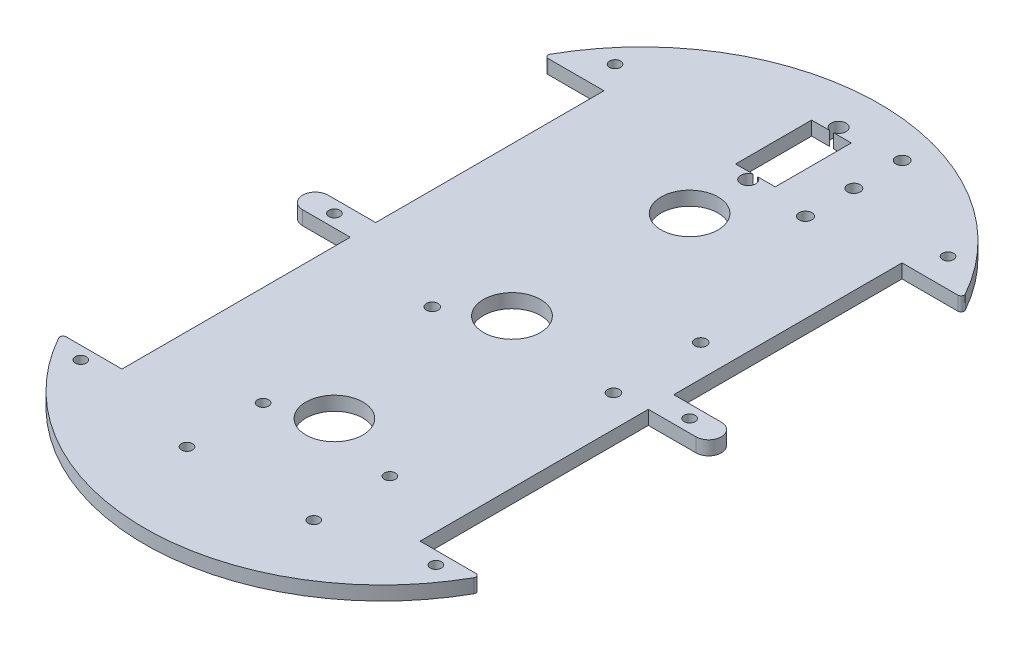
SolidWorks part; units mm, degrees
material "ABS PC"
ref_plane "Front Plane" through (0, 0, 0) normal (0, 0, 1) x (1, 0, 0)
ref_plane "Top Plane" through (0, 0, 0) normal (0, 1, 0) x (1, 0, 0)
ref_plane "Right Plane" through (0, 0, 0) normal (1, 0, 0) x (0, 0, -1)
sketch "Sketch2" plane through (0, 0, 0) normal (0, 1, 0) x (1, 0, 0)
  line L1 (-66, 116) -> (66, 116)
  line L2 (-66, 116) -> (-66, -116)
  line L3 (-66, -116) -> (66, -116)
  line L4 (66, 116) -> (66, -116)
  point P4 (66, 0)
  point P6 (0, 116)
  dimension "D1" = 132
  dimension "D2" = 232
extrude "Plate Size" add sketch "Sketch2" along normal blind 4.4
sketch "Sketch4" plane through (0, 0, 0) normal (0, 1, 0) x (1, 0, 0)
  line L0 (-66, 116) -> (-66, -116) construction
  line L1 (66, 116) -> (66, -116) construction
  line L2 (0, -40.9051) -> (0, 40.9051) construction
  line L4 (-64.6, 76) -> (-47, 76)
  line L6 (-62, 4) -> (-47, 4)
  line L7 (-47, 76) -> (-47, 4)
  line L8 (-47, -4) -> (-47, 4) construction
  line L9 (64.6, 76) -> (47, 76)
  line L11 (62, 4) -> (47, 4)
  line L12 (47, 76) -> (47, 4)
  line L13 (64.6, -76) -> (47, -76)
  line L15 (62, -4) -> (47, -4)
  line L16 (47, -76) -> (47, -4)
  line L17 (-47, -76) -> (-64.6, -76)
  line L18 (-47, -76) -> (-47, -4)
  line L19 (-47, -4) -> (-62, -4)
  line L21 (47, -4) -> (47, 4) construction
  line L23 (-47, 40) -> (47, 40) construction
  line L24 (0, -2.475) -> (0, 2.475) construction
  arc A0 (65.473, 77.4878) -> (-65.473, 77.4878) centre (0, 40.9051) ccw
  arc A1 (-65.473, -77.4878) -> (65.473, -77.4878) centre (0, -40.9051) ccw
  arc A2 (-62, 4) -> (-62, -4) centre (-62, 0) ccw
  arc A3 (62, -4) -> (62, 4) centre (62, 0) ccw
  arc A4 (-64.6, -76) -> (-65.473, -77.4878) centre (-64.6, -77) ccw
  arc A5 (65.473, -77.4878) -> (64.6, -76) centre (64.6, -77) ccw
  arc A6 (64.6, 76) -> (65.473, 77.4878) centre (64.6, 77) ccw
  arc A7 (-65.473, 77.4878) -> (-64.6, 76) centre (-64.6, 77) ccw
  point P2 (0, 0)
  point P33 (-47, 0)
  point P39 (0, 40)
  dimension "D1" = 150
  dimension "D2" = 231.8102
  dimension "D6" = 2
  dimension "D3" = 72
  dimension "D4" = 8
  dimension "D5" = 94
extrude "Outer Profile" cut sketch "Sketch4" along normal through all flip side to cut
hole_wizard "M3 Clearance Hole1" positions "Sketch5" profile "Sketch6" hole size "M3" standard "ANSI Metric" end condition through all
sketch "Sketch5" plane through (0, 0, 0) normal (0, 1, 0) x (1, 0, 0)
  line L1 (-56, -80) -> (56, -80) construction
  line L5 (0, -2.42) -> (0, 2.42) construction
  line L7 (-2.42, 0) -> (2.42, 0) construction
  line L8 (-52.5, 85) -> (52.5, 85) construction
  line L10 (56, 0) -> (-56, 0) construction
  circle A0 centre (-56, -80) radius 1.75 construction
  point P0 (-56, -80)
  point P159 (56, -80)
  point P161 (0, -80)
  point P171 (-52.5, 85)
  point P177 (52.5, 85)
  point P179 (0, 85)
  point P184 (-56, 0)
  point P186 (56, 0)
  point P192 (0, 0)
  dimension "D1" = 80
  dimension "D3" = 3.5
  dimension "D2" = 56
  dimension "D4" = 52.5
  dimension "D5" = 85
sketch "Sketch6" plane through (-56, 0, 80) normal (1, 0, 0) x (0, 0, -1)
  line L0 (0, 0) -> (0, 4.4)
  line L1 (0, 4.4) -> (1.75, 4.4)
  line L2 (1.75, 4.4) -> (1.75, 0)
  line L5 (1.75, 0) -> (0, 0)
  line L11 (0, -6.35) -> (0, 107.95) construction
  dimension "Thru Hole Dia." = 3.5
  dimension "Thru Hole Depth" = 4.4
hole_wizard "Ø18.0 (18) Diameter Hole4" positions "Sketch9" profile "Sketch10" hole size "Ø18.0" standard "ANSI Metric" end condition through all
sketch "Sketch9" plane through (0, 0, 0) normal (0, 1, 0) x (1, 0, 0)
  line L0 (0, -2.42) -> (0, 2.42) construction
  line L1 (0, -56) -> (0, 56) construction
  line L3 (-2.42, 0) -> (2.42, 0) construction
  point P0 (0, 56)
  point P2 (0, -56)
  point P10 (0, 0)
  dimension "D1" = 56
sketch "Sketch10" plane through (0, 0, -56) normal (1, 0, 0) x (0, 0, -1)
  line L0 (0, 0) -> (0, 4.4)
  line L1 (0, 4.4) -> (9, 4.4)
  line L2 (9, 4.4) -> (9, 0)
  line L5 (9, 0) -> (0, 0)
  line L11 (0, -6.35) -> (0, 107.95) construction
  dimension "Thru Hole Dia." = 18
  dimension "Thru Hole Depth" = 4.4
hole_wizard "M3 Clearance Hole2" positions "Sketch11" profile "Sketch12" hole size "M3" standard "ANSI Metric" end condition through all
sketch "Sketch11" plane through (0, 0, 0) normal (0, 1, 0) x (1, 0, 0)
  line L1 (24.5, -87) -> (-15.5, -87) construction
  line L2 (24.5, -87) -> (24.5, -63) construction
  line L3 (24.5, -63) -> (-15.5, -63) construction
  line L4 (-15.5, -87) -> (-15.5, -63) construction
  line L5 (0, -2.42) -> (0, 2.42) construction
  line L7 (-2.42, 0) -> (2.42, 0) construction
  circle A0 centre (24.5, -87) radius 2 construction
  circle A1 centre (-15.5, -63) radius 2 construction
  point P0 (24.5, -87)
  point P2 (-15.5, -63)
  point P110 (-15.5, -87)
  point P113 (24.5, -63)
  dimension "D1" = 4
  dimension "D3" = 87
  dimension "D2" = 24.5
  dimension "D4" = 24
  dimension "D5" = 40
sketch "Sketch12" plane through (24.5, 0, 87) normal (1, 0, 0) x (0, 0, -1)
  line L0 (0, 0) -> (0, 4.4)
  line L1 (0, 4.4) -> (1.75, 4.4)
  line L2 (1.75, 4.4) -> (1.75, 0)
  line L5 (1.75, 0) -> (0, 0)
  line L11 (0, -6.35) -> (0, 107.95) construction
  dimension "Thru Hole Dia." = 3.5
  dimension "Thru Hole Depth" = 4.4
sketch "Sketch13" plane through (0, 0, 0) normal (0, 1, 0) x (1, 0, 0)
  line L0 (-2.475, 0) -> (2.475, 0) construction
  line L1 (-6.25, 100.75) -> (6.25, 100.75)
  line L2 (-6.25, 100.75) -> (-6.25, 76.75)
  line L3 (-6.25, 76.75) -> (6.25, 76.75)
  line L4 (6.25, 100.75) -> (6.25, 76.75)
  line L5 (0, -2.475) -> (0, 2.475) construction
  point P8 (0, 76.75)
  dimension "D1" = 24
  dimension "D2" = 12.5
  dimension "D3" = 76.75
extrude "Servo Clearance" cut sketch "Sketch13" along normal through all
hole_wizard "M3 Head Clearance Hole3" positions "Sketch14" profile "Sketch15" hole size "M3" standard "ANSI Metric" end condition through all
sketch "Sketch14" plane through (0, 0, 0) normal (0, 1, 0) x (1, 0, 0)
  line L0 (0, -2.42) -> (0, 2.42) construction
  line L1 (-2.42, 0) -> (2.42, 0) construction
  circle A0 centre (0, 74.5) radius 2.3489 construction
  point P0 (0, 103)
  point P2 (0, 74.5)
  dimension "D3" = 4.6979
  dimension "D1" = 74.5
  dimension "D2" = 28.5
sketch "Sketch15" plane through (0, 0, -103) normal (1, 0, 0) x (0, 0, -1)
  line L0 (0, 0) -> (0, 4.4)
  line L1 (0, 4.4) -> (2.35, 4.4)
  line L2 (2.35, 4.4) -> (2.35, 0)
  line L5 (2.35, 0) -> (0, 0)
  line L11 (0, -6.35) -> (0, 107.95) construction
  dimension "Thru Hole Dia." = 4.7
  dimension "Thru Hole Depth" = 4.4
hole_wizard "M3 Clearance Hole4" positions "Sketch16" profile "Sketch17" hole size "M3" standard "ANSI Metric" end condition through all
sketch "Sketch16" plane through (0, 0, 0) normal (0, 1, 0) x (1, 0, 0)
  line L0 (19.055, 73.5) -> (19.055, 104) construction
  line L2 (-2.42, 0) -> (2.42, 0) construction
  line L3 (0, -2.42) -> (0, 2.42) construction
  circle A0 centre (19.055, 73.5) radius 2 construction
  point P0 (19.055, 73.5)
  point P2 (19.055, 88.75)
  point P4 (19.055, 104)
  dimension "D2" = 4
  dimension "D1" = 30.5
  dimension "D3" = 73.5
  dimension "D4" = 19.055
sketch "Sketch17" plane through (19.055, 0, -73.5) normal (1, 0, 0) x (0, 0, -1)
  line L0 (0, 0) -> (0, 4.4)
  line L1 (0, 4.4) -> (2, 4.4)
  line L2 (2, 4.4) -> (2, 0)
  line L5 (2, 0) -> (0, 0)
  line L11 (0, -6.35) -> (0, 107.95) construction
  dimension "Thru Hole Dia." = 4
  dimension "Thru Hole Depth" = 4.4
hole_wizard "M3 Clearance Hole5" positions "Sketch18" profile "Sketch19" hole size "M3" standard "ANSI Metric" end condition through all
sketch "Sketch18" plane through (0, 0, 0) normal (0, 1, 0) x (1, 0, 0)
  line L5 (-2.42, 0) -> (2.42, 0) construction
  line L6 (0, -2.42) -> (0, 2.42) construction
  circle A0 centre (37, 22.5) radius 1.85 construction
  point P0 (37, 22.5)
  point P2 (-15.07, -10.08)
  point P101 (37, -5)
  dimension "D1" = 22.5
  dimension "D3" = 3.7
  dimension "D2" = 37
  dimension "D4" = 5
  dimension "D5" = 52.07
  dimension "D6" = 5.08
sketch "Sketch19" plane through (37, 0, -22.5) normal (1, 0, 0) x (0, 0, -1)
  line L0 (0, 0) -> (0, 4.4)
  line L1 (0, 4.4) -> (1.85, 4.4)
  line L2 (1.85, 4.4) -> (1.85, 0)
  line L5 (1.85, 0) -> (0, 0)
  line L11 (0, -6.35) -> (0, 107.95) construction
  dimension "Thru Hole Dia." = 3.7
  dimension "Thru Hole Depth" = 4.4
sketch "Sketch20" plane through (0, 4.4, 0) normal (0, 1, 0) x (1, 0, 0)
  circle A0 centre (0, 0) radius 9.017
  dimension "D1" = 18.034
extrude "Cut-Extrude1" cut sketch "Sketch20" against normal blind 6.35
